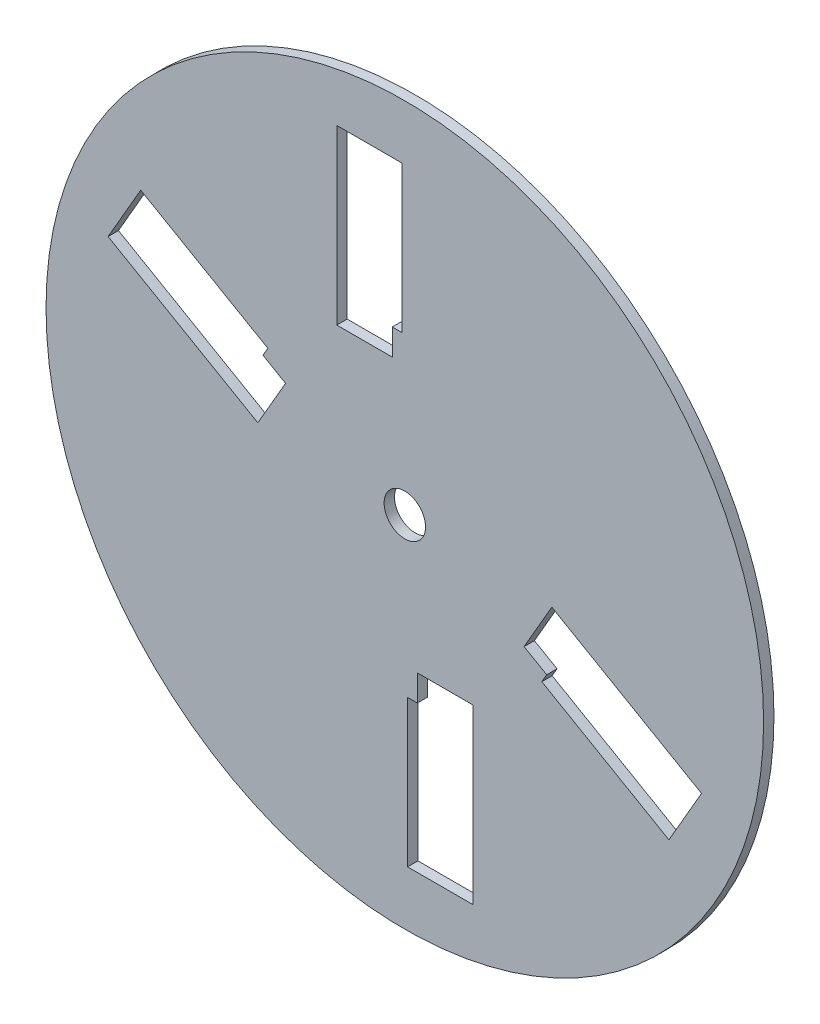
SolidWorks part; units mm, degrees
ref_plane "Front Plane" through (0, 0, 0) normal (0, 0, 1) x (1, 0, 0)
ref_plane "Top Plane" through (0, 0, 0) normal (0, 1, 0) x (1, 0, 0)
ref_plane "Right Plane" through (0, 0, 0) normal (1, 0, 0) x (0, 0, -1)
sketch "Sketch1" plane through (0, 0, 0) normal (0, 0, 1) x (1, 0, 0)
  line L0 (-6.35, 0) -> (-6.35, 42.8001) construction
  line L1 (-6.35, 40) -> (-3.85, 40)
  line L2 (-3.85, 40) -> (-3.85, 48)
  line L3 (-3.85, 48) -> (-0.85, 48)
  line L4 (-0.85, 48) -> (-0.85, 93)
  line L5 (-0.85, 93) -> (-20.85, 93)
  line L6 (-20.85, 93) -> (-20.85, 40)
  line L7 (-20.85, 40) -> (-18.35, 40)
  line L8 (-18.35, 40) -> (-6.35, 40)
  line L9 (-6.35, 40) -> (-6.35, 0)
  line L10 (6.35, -40) -> (3.85, -40)
  line L11 (3.85, -40) -> (3.85, -48)
  line L12 (3.85, -48) -> (0.85, -48)
  line L13 (0.85, -48) -> (0.85, -93)
  line L14 (0.85, -93) -> (20.85, -93)
  line L15 (20.85, -93) -> (20.85, -40)
  line L16 (20.85, -40) -> (18.35, -40)
  line L17 (18.35, -40) -> (6.35, -40)
  line L18 (-3.85, 40) -> (3.85, -40) construction
  line L19 (37.816, -14.5007) -> (36.566, -16.6658)
  line L20 (36.566, -16.6658) -> (43.4942, -20.6658)
  line L21 (43.4942, -20.6658) -> (41.9942, -23.2639)
  line L22 (41.9942, -23.2639) -> (80.9654, -45.7639)
  line L23 (80.9654, -45.7639) -> (90.9654, -28.4434)
  line L24 (90.9654, -28.4434) -> (45.066, -1.9434)
  line L25 (45.066, -1.9434) -> (43.816, -4.1084)
  line L26 (43.816, -4.1084) -> (37.816, -14.5007)
  line L27 (0, 0) -> (3.85, -40) construction
  line L28 (0, 0) -> (36.566, -16.6658) construction
  line L29 (-37.816, 14.5007) -> (-36.566, 16.6658)
  line L30 (-36.566, 16.6658) -> (-43.4942, 20.6658)
  line L31 (-43.4942, 20.6658) -> (-41.9942, 23.2639)
  line L32 (-41.9942, 23.2639) -> (-80.9654, 45.7639)
  line L33 (-80.9654, 45.7639) -> (-90.9654, 28.4434)
  line L34 (-90.9654, 28.4434) -> (-45.066, 1.9434)
  line L35 (-45.066, 1.9434) -> (-43.816, 4.1084)
  line L36 (-43.816, 4.1084) -> (-37.816, 14.5007)
  line L37 (-36.566, 16.6658) -> (0, 0) construction
  circle A0 centre (0, 0) radius 110
  circle A1 centre (0, 0) radius 6.35
  point P14 (-6.35, 0)
  point P27 (0, 0)
  point P46 (0, 0)
  dimension "D5" = 12.7
  dimension "D11" = 220
  dimension "D1" = 17
  dimension "D2" = 12
  dimension "D3" = 53
  dimension "D4" = 45
  dimension "D6" = 20
  dimension "D7" = 40
  dimension "D10" = 60
  dimension "D8" = 2
  dimension "D9" = 2
  dimension "D12" = 2
extrude "Boss-Extrude1" add sketch "Sketch1" along normal mid plane 3.175
